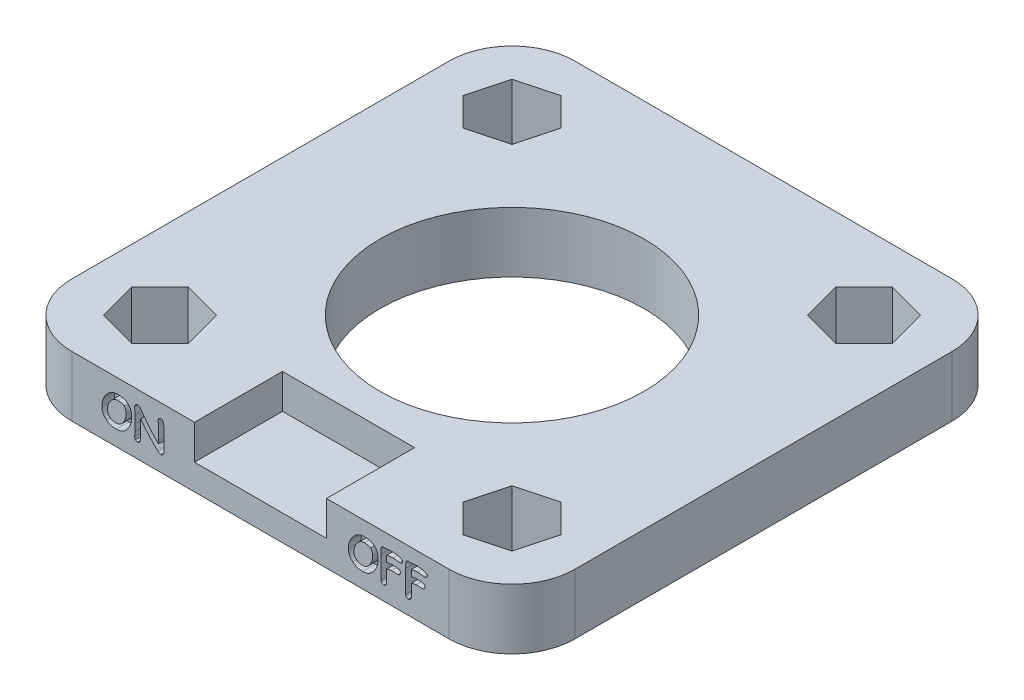
SolidWorks part; units mm, degrees
ref_plane "Přední rovina" through (0, 0, 0) normal (0, 0, 1) x (1, 0, 0)
ref_plane "Horní rovina" through (0, 0, 0) normal (0, 1, 0) x (1, 0, 0)
ref_plane "Pravá rovina" through (0, 0, 0) normal (1, 0, 0) x (0, 0, -1)
sketch "Skica1" plane through (0, 0, 0) normal (0, 1, 0) x (1, 0, 0)
  line L1 (20, 20) -> (-20, 20)
  line L2 (20, 20) -> (20, -20)
  line L3 (20, -20) -> (-20, -20)
  line L4 (-20, 20) -> (-20, -20)
  line L5 (20, 20) -> (-20, -20) construction
  line L6 (20, -20) -> (-20, 20) construction
  line L7 (-11.7546, 11.7546) -> (-10.9328, 14.8219)
  line L8 (-10.9328, 14.8219) -> (-13.1781, 17.0672)
  line L9 (-13.1781, 17.0672) -> (-16.2454, 16.2454)
  line L10 (-16.2454, 16.2454) -> (-17.0672, 13.1781)
  line L11 (-17.0672, 13.1781) -> (-14.8219, 10.9328)
  line L12 (-14.8219, 10.9328) -> (-11.7546, 11.7546)
  line L13 (16.2454, 16.2454) -> (13.1781, 17.0672)
  line L14 (13.1781, 17.0672) -> (10.9328, 14.8219)
  line L15 (10.9328, 14.8219) -> (11.7546, 11.7546)
  line L16 (11.7546, 11.7546) -> (14.8219, 10.9328)
  line L17 (14.8219, 10.9328) -> (17.0672, 13.1781)
  line L18 (17.0672, 13.1781) -> (16.2454, 16.2454)
  line L19 (16.2454, -16.2454) -> (17.0672, -13.1781)
  line L20 (17.0672, -13.1781) -> (14.8219, -10.9328)
  line L21 (14.8219, -10.9328) -> (11.7546, -11.7546)
  line L22 (11.7546, -11.7546) -> (10.9328, -14.8219)
  line L23 (10.9328, -14.8219) -> (13.1781, -17.0672)
  line L24 (13.1781, -17.0672) -> (16.2454, -16.2454)
  line L25 (-16.2454, -16.2454) -> (-13.1781, -17.0672)
  line L26 (-13.1781, -17.0672) -> (-10.9328, -14.8219)
  line L27 (-10.9328, -14.8219) -> (-11.7546, -11.7546)
  line L28 (-11.7546, -11.7546) -> (-14.8219, -10.9328)
  line L29 (-14.8219, -10.9328) -> (-17.0672, -13.1781)
  line L30 (-17.0672, -13.1781) -> (-16.2454, -16.2454)
  circle A0 centre (0, 0) radius 10.5
  circle A1 centre (-14, 14) radius 1.5 construction
  circle A2 centre (-14, -14) radius 1.5 construction
  circle A3 centre (14, -14) radius 1.5 construction
  circle A4 centre (14, 14) radius 1.5 construction
  circle A5 centre (-14, 14) radius 2.75 construction
  circle A6 centre (14, 14) radius 2.75 construction
  circle A7 centre (14, -14) radius 2.75 construction
  circle A8 centre (-14, -14) radius 2.75 construction
  point P0 (0, 0)
  dimension "D3" = 21
  dimension "D4" = 3
  dimension "D5" = 3
  dimension "D6" = 3
  dimension "D7" = 3
  dimension "D1" = 40
  dimension "D2" = 40
  dimension "D8" = 6
  dimension "D9" = 6
  dimension "D10" = 6
  dimension "D11" = 6
  dimension "D12" = 6
  dimension "D13" = 6
  dimension "D14" = 6
  dimension "D15" = 6
  dimension "D16" = 5.5
  dimension "D17" = 5.5
  dimension "D18" = 5.5
  dimension "D19" = 5.5
extrude "Přidat vysunutím1" add sketch "Skica1" along normal blind 4.8
fillet "Zaoblit1" radius 5 4 edges at (20, 2.4, 20) (20, 2.4, -20) (-20, 2.4, -20) (-20, 2.4, 20)
sketch "Skica2" plane through (0, 0, 20) normal (0, 0, 1) x (1, 0, 0)
  line L0 (-15, 4.8) -> (15, 4.8) construction
  line L1 (5.25, 7.55) -> (-5.25, 7.55)
  line L2 (5.25, 7.55) -> (5.25, 2.05)
  line L3 (5.25, 2.05) -> (-5.25, 2.05)
  line L4 (-5.25, 7.55) -> (-5.25, 2.05)
  line L5 (5.25, 7.55) -> (-5.25, 2.05) construction
  line L6 (5.25, 2.05) -> (-5.25, 7.55) construction
  point P0 (0, 4.8)
  dimension "D1" = 5.5
  dimension "D2" = 10.5
extrude "Odebrat vysunutím1" cut sketch "Skica2" against normal blind 7
sketch "Skica4" plane through (0, 0, 20) normal (0, 0, 1) x (1, 0, 0)
  line L0 (-5.25, 1.3) -> (-15, 1.3) construction
  line L4 (-5.25, 2.05) -> (-5.25, 4.8) construction
  line L5 (-15, 4.8) -> (-15, 0) construction
  line L6 (5.25, 1.3) -> (15, 1.3) construction
  line L7 (5.25, 2.05) -> (5.25, 4.8) construction
  line L8 (15, 0) -> (15, 4.8) construction
  line L9 (-15, 0) -> (15, 0) construction
  text T0 "ON" font "Comic Sans MS" height 2.4
  text T1 "OFF" font "Comic Sans MS" height 2.4
  dimension "D1" = 1.3
  dimension "D2" = 1.3
extrude "Odebrat vysunutím2" cut sketch "Skica4" against normal blind 1
